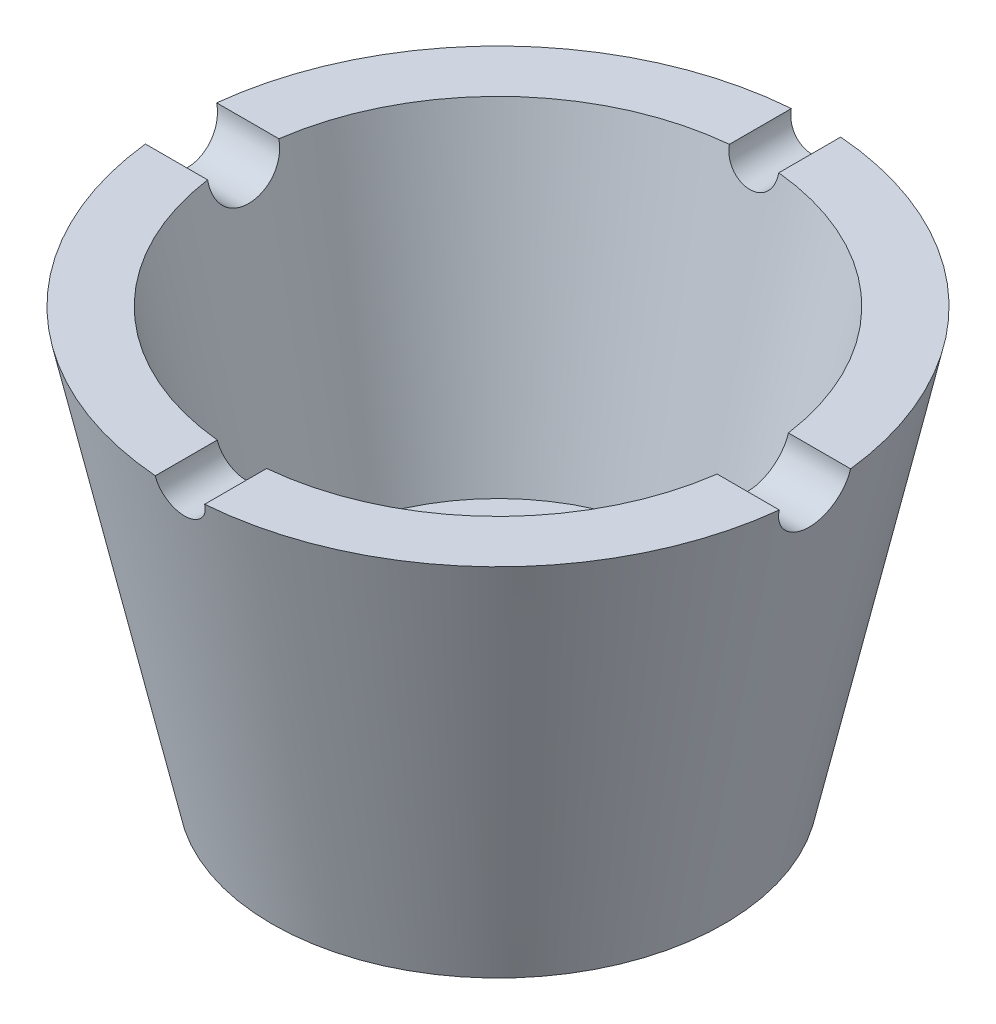
SolidWorks part; units mm, degrees
ref_plane "Front Plane" through (0, 0, 0) normal (0, 0, 1) x (1, 0, 0)
ref_plane "Top Plane" through (0, 0, 0) normal (0, 1, 0) x (1, 0, 0)
ref_plane "Right Plane" through (0, 0, 0) normal (1, 0, 0) x (0, 0, -1)
sketch "Sketch1" plane through (0, 0, 0) normal (0, 0, 1) x (1, 0, 0)
  line L0 (0, 29.1369) -> (0, -23.266) construction
  line L1 (11.25, 10.83) -> (11.25, -1.17)
  line L2 (11.25, -1.17) -> (22.5, -1.17)
  line L3 (22.5, -1.17) -> (31.7537, 40.83)
  line L4 (31.7537, 40.83) -> (25.6098, 40.83)
  line L5 (25.6098, 40.83) -> (19, 10.83)
  line L6 (19, 10.83) -> (11.25, 10.83)
  line L7 (19, 21.2076) -> (19, 7.3878) construction
  dimension "D1" = 11.25
  dimension "D2" = 22.5
  dimension "D3" = 42
  dimension "D4" = 12
  dimension "D5" = 6
  dimension "D6" = 19
revolve "Revolve1" add sketch "Sketch1" angle 360 about L0
sketch "Sketch2" plane through (0, 0, 0) normal (1, 0, 0) x (0, 0, -1)
  line L0 (-3.5478, 40.83) -> (3.5478, 40.83)
  arc A0 (-3.5478, 40.83) -> (3.5478, 40.83) centre (0, 40.83) ccw
extrude "Cut-Extrude1" cut sketch "Sketch2" against normal mid plane 100
sketch "Sketch3" plane through (0, 0, 0) normal (0, 0, 1) x (1, 0, 0)
  line L0 (31.5548, 40.83) -> (-31.5548, 40.83) construction
  line L1 (-2.457, 40.83) -> (2.457, 40.83)
  arc A0 (-2.457, 40.83) -> (2.457, 40.83) centre (0, 40.83) ccw
extrude "Cut-Extrude2" cut sketch "Sketch3" against normal mid plane 100
